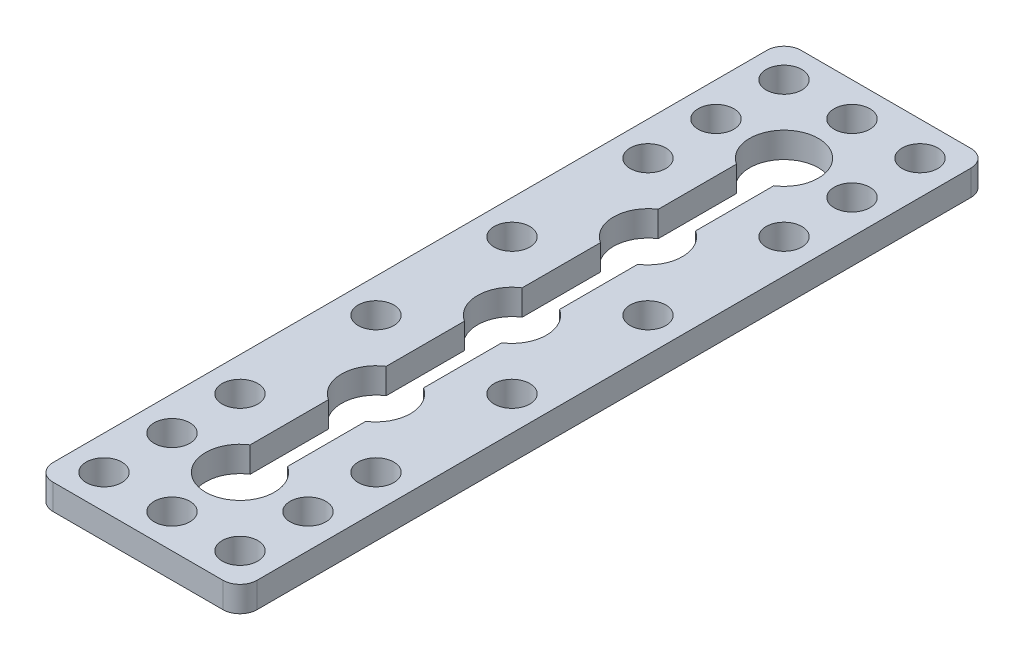
SolidWorks part; units mm, degrees
ref_plane "Front Plane" through (0, 0, 0) normal (0, 0, 1) x (1, 0, 0)
ref_plane "Top Plane" through (0, 0, 0) normal (0, 1, 0) x (1, 0, 0)
ref_plane "Right Plane" through (0, 0, 0) normal (1, 0, 0) x (0, 0, -1)
sketch "Sketch1" plane through (0, 0, 0) normal (0, 1, 0) x (1, 0, 0)
  line L1 (0, 0) -> (24, 0)
  line L2 (0, 0) -> (0, 88)
  line L3 (0, 88) -> (24, 88)
  line L4 (24, 0) -> (24, 88)
  dimension "D1" = 24
  dimension "D2" = 88
extrude "Boss-Extrude1" add sketch "Sketch1" along normal blind 3
sketch "Sketch2" plane through (0, 3, 0) normal (0, 1, 0) x (1, 0, 0)
  line L0 (12, 0) -> (12, 88) construction
  line L1 (0, 0) -> (24, 0) construction
  line L2 (24, 88) -> (0, 88) construction
  line L3 (0, 44) -> (24, 44) construction
  line L4 (0, 88) -> (0, 0) construction
  line L5 (24, 0) -> (24, 88) construction
  line L6 (4, 88) -> (4, 44) construction
  line L7 (4, 84) -> (12, 84) construction
  line L8 (4, 76) -> (12, 76) construction
  line L9 (4, 12) -> (12, 12) construction
  line L10 (4, 4) -> (12, 4) construction
  circle A0 centre (12, 84) radius 2.1
  circle A1 centre (4, 84) radius 2.1
  circle A2 centre (4, 76) radius 2.1
  circle A3 centre (4, 68) radius 2.1
  circle A4 centre (4, 52) radius 2.1
  circle A6 centre (20, 52) radius 2.1
  circle A7 centre (20, 68) radius 2.1
  circle A8 centre (20, 76) radius 2.1
  circle A9 centre (20, 84) radius 2.1
  circle A10 centre (20, 4) radius 2.1
  circle A11 centre (20, 12) radius 2.1
  circle A12 centre (20, 20) radius 2.1
  circle A13 centre (20, 36) radius 2.1
  circle A14 centre (4, 36) radius 2.1
  circle A15 centre (4, 20) radius 2.1
  circle A16 centre (4, 12) radius 2.1
  circle A17 centre (4, 4) radius 2.1
  circle A18 centre (12, 4) radius 2.1
  dimension "D1" = 4.2
  dimension "D2" = 16
  dimension "D3" = 16
  dimension "D4" = 8
  dimension "D5" = 16
  dimension "D6" = 16
extrude "Cut-Extrude1" cut sketch "Sketch2" against normal through all
sketch "Sketch3" plane through (0, 3, 0) normal (0, 1, 0) x (1, 0, 0)
  circle A0 centre (12, 76) radius 4.05
  dimension "D1" = 8.1
extrude "Cut-Extrude2" cut sketch "Sketch3" against normal through all
pattern_linear "LPattern1" count 5 spacing 16 along (0, 0, 1) of "Cut-Extrude2"
sketch "Sketch4" plane through (0, 3, 0) normal (0, 1, 0) x (1, 0, 0)
  line L1 (9.8, 76) -> (14.2, 76)
  line L2 (9.8, 76) -> (9.8, 12)
  line L3 (9.8, 12) -> (14.2, 12)
  line L4 (14.2, 76) -> (14.2, 12)
  point P4 (12, 76)
  point P6 (12, 12)
  dimension "D1" = 4.4
extrude "Cut-Extrude3" cut sketch "Sketch4" against normal through all
fillet "Fillet1" radius 2 4 edges at (24, 1.5, -88) (0, 1.5, -88) (0, 1.5, 0) (24, 1.5, 0)
equation "\"width\"= 24"
equation "\"thk\"= 3"
equation "\"holesize\"= 4.2"
equation "\"holedistance\"= ( 20 + 12 ) / 2"
equation "\"threaded_hole\"= 3.9"
equation "\"fillet_radius\"= 2"
equation "\"D1@Sketch1\"=\"width\""
equation "\"D1@Boss-Extrude1\"=\"thk\""
equation "\"D1@Sketch2\"=\"holesize\""
equation "\"D2@Sketch2\"=\"holedistance\""
equation "\"D3@Sketch2\"=\"holedistance\""
equation "\"D4@Sketch2\"=\"holedistance\"/2"
equation "\"D5@Sketch2\"=\"holedistance\""
equation "\"D6@Sketch2\"=\"holedistance\""
equation "\"D1@Fillet1\"=\"fillet_radius\""
equation "\"ground_clearance\"= 25"
equation "\"tire_thk\"= 3"
equation "\"innerwheel_diam\" = \"wheel_diam\"-2*\"tire_thk\""
equation "\"innerwheel_thk\"= 8"
equation "\"wheel_diam\"= 2*(\"width\"/2+\"ground_clearance\")"
equation "\"coloursensor_holesize\"= 2.65"
equation "\"hole_to_edge\" = 4"
